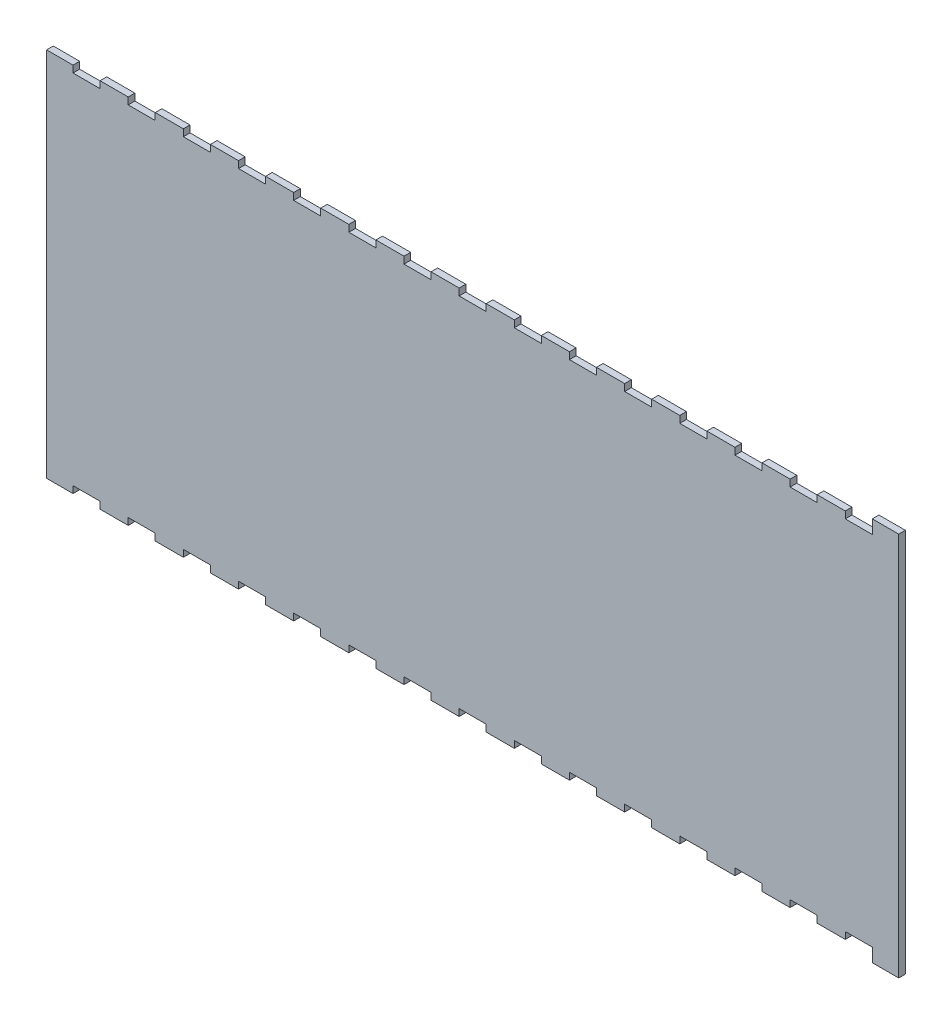
SolidWorks part; units mm, degrees
ref_plane "Front Plane" through (0, 0, 0) normal (0, 0, 1) x (1, 0, 0)
ref_plane "Top Plane" through (0, 0, 0) normal (0, 1, 0) x (1, 0, 0)
ref_plane "Right Plane" through (0, 0, 0) normal (1, 0, 0) x (0, 0, -1)
sketch "Sketch1" plane through (0, 0, 0) normal (0, 0, 1) x (1, 0, 0)
  line L248 (-12.6, 173.7122) -> (-25.5, 173.7122)
  line L249 (-25.5, 173.7122) -> (-25.5, 176.9872)
  line L250 (-25.5, 176.9872) -> (-38.9071, 176.9872)
  line L251 (-38.9071, 176.9872) -> (-38.9071, 173.7122)
  line L252 (-38.9071, 173.7122) -> (-51.8071, 173.7122)
  line L253 (-51.8071, 173.7122) -> (-51.8071, 176.9872)
  line L254 (-51.8071, 176.9872) -> (-65.2143, 176.9872)
  line L255 (-65.2143, 176.9872) -> (-65.2143, 173.7122)
  line L256 (-65.2143, 173.7122) -> (-78.1143, 173.7122)
  line L257 (-78.1143, 173.7122) -> (-78.1143, 176.9872)
  line L258 (-78.1143, 176.9872) -> (-91.5214, 176.9872)
  line L259 (-91.5214, 176.9872) -> (-91.5214, 173.7122)
  line L260 (-91.5214, 173.7122) -> (-104.4214, 173.7122)
  line L261 (-104.4214, 173.7122) -> (-104.4214, 176.9872)
  line L262 (-104.4214, 176.9872) -> (-117.8286, 176.9872)
  line L263 (-117.8286, 176.9872) -> (-117.8286, 173.7122)
  line L264 (-117.8286, 173.7122) -> (-130.7286, 173.7122)
  line L265 (-130.7286, 173.7122) -> (-130.7286, 176.9872)
  line L266 (-130.7286, 176.9872) -> (-144.1357, 176.9872)
  line L267 (-144.1357, 176.9872) -> (-144.1357, 173.7122)
  line L268 (-144.1357, 173.7122) -> (-157.0357, 173.7122)
  line L269 (-157.0357, 173.7122) -> (-157.0357, 176.9872)
  line L270 (-157.0357, 176.9872) -> (-170.4429, 176.9872)
  line L271 (-170.4429, 176.9872) -> (-170.4429, 173.7122)
  line L272 (-170.4429, 173.7122) -> (-183.3429, 173.7122)
  line L273 (-183.3429, 173.7122) -> (-183.3429, 176.9872)
  line L274 (-183.3429, 176.9872) -> (-196.75, 176.9872)
  line L275 (-196.75, 176.9872) -> (-196.75, 173.7122)
  line L276 (-196.75, 173.7122) -> (-209.65, 173.7122)
  line L277 (-209.65, 173.7122) -> (-209.65, 176.9872)
  line L278 (-209.65, 176.9872) -> (-223.0571, 176.9872)
  line L279 (-223.0571, 176.9872) -> (-223.0571, 173.7122)
  line L280 (-223.0571, 173.7122) -> (-235.9571, 173.7122)
  line L281 (-235.9571, 173.7122) -> (-235.9571, 176.9872)
  line L282 (-235.9571, 176.9872) -> (-249.3643, 176.9872)
  line L283 (-249.3643, 176.9872) -> (-249.3643, 173.7122)
  line L284 (-249.3643, 173.7122) -> (-262.2643, 173.7122)
  line L285 (-262.2643, 173.7122) -> (-262.2643, 176.9872)
  line L286 (-262.2643, 176.9872) -> (-275.6714, 176.9872)
  line L287 (-275.6714, 176.9872) -> (-275.6714, 173.7122)
  line L288 (-275.6714, 173.7122) -> (-288.5714, 173.7122)
  line L289 (-288.5714, 173.7122) -> (-288.5714, 176.9872)
  line L290 (-288.5714, 176.9872) -> (-301.9786, 176.9872)
  line L291 (-301.9786, 176.9872) -> (-301.9786, 173.7122)
  line L292 (-301.9786, 173.7122) -> (-314.8786, 173.7122)
  line L293 (-314.8786, 173.7122) -> (-314.8786, 176.9872)
  line L294 (-314.8786, 176.9872) -> (-328.2857, 176.9872)
  line L295 (-328.2857, 176.9872) -> (-328.2857, 173.7122)
  line L296 (-328.2857, 173.7122) -> (-341.1857, 173.7122)
  line L297 (-341.1857, 173.7122) -> (-341.1857, 176.9872)
  line L298 (-341.1857, 176.9872) -> (-354.5929, 176.9872)
  line L299 (-354.5929, 176.9872) -> (-354.5929, 173.7122)
  line L300 (-354.5929, 173.7122) -> (-367.4929, 173.7122)
  line L301 (-367.4929, 173.7122) -> (-367.4929, 176.9872)
  line L302 (-367.4929, 176.9872) -> (-380.9, 176.9872)
  line L303 (-380.9, 176.9872) -> (-380.9, 173.7122)
  line L304 (-380.9, 173.7122) -> (-393.8, 173.7122)
  line L305 (-393.8, 173.7122) -> (-393.8, 176.9872)
  line L306 (-393.8, 176.9872) -> (-406.4, 176.9872)
  line L307 (-406.4, 176.9872) -> (-406.4, 0)
  line L308 (-406.4, 0) -> (-393.8, 0)
  line L309 (-393.8, 0) -> (-393.8, 3.275)
  line L310 (-393.8, 3.275) -> (-380.9, 3.275)
  line L311 (-380.9, 3.275) -> (-380.9, 0)
  line L312 (-380.9, 0) -> (-367.4929, 0)
  line L313 (-367.4929, 0) -> (-367.4929, 3.275)
  line L314 (-367.4929, 3.275) -> (-354.5929, 3.275)
  line L315 (-354.5929, 3.275) -> (-354.5929, 0)
  line L316 (-354.5929, 0) -> (-341.1857, 0)
  line L317 (-341.1857, 0) -> (-341.1857, 3.275)
  line L318 (-341.1857, 3.275) -> (-328.2857, 3.275)
  line L319 (-328.2857, 3.275) -> (-328.2857, 0)
  line L320 (-328.2857, 0) -> (-314.8786, 0)
  line L321 (-314.8786, 0) -> (-314.8786, 3.275)
  line L322 (-314.8786, 3.275) -> (-301.9786, 3.275)
  line L323 (-301.9786, 3.275) -> (-301.9786, 0)
  line L324 (-301.9786, 0) -> (-288.5714, 0)
  line L325 (-288.5714, 0) -> (-288.5714, 3.275)
  line L326 (-288.5714, 3.275) -> (-275.6714, 3.275)
  line L327 (-275.6714, 3.275) -> (-275.6714, 0)
  line L328 (-275.6714, 0) -> (-262.2643, 0)
  line L329 (-262.2643, 0) -> (-262.2643, 3.275)
  line L330 (-262.2643, 3.275) -> (-249.3643, 3.275)
  line L331 (-249.3643, 3.275) -> (-249.3643, 0)
  line L332 (-249.3643, 0) -> (-235.9571, 0)
  line L333 (-235.9571, 0) -> (-235.9571, 3.275)
  line L334 (-235.9571, 3.275) -> (-223.0571, 3.275)
  line L335 (-223.0571, 3.275) -> (-223.0571, 0)
  line L336 (-223.0571, 0) -> (-209.65, 0)
  line L337 (-209.65, 0) -> (-209.65, 3.275)
  line L338 (-209.65, 3.275) -> (-196.75, 3.275)
  line L339 (-196.75, 3.275) -> (-196.75, 0)
  line L340 (-196.75, 0) -> (-183.3429, 0)
  line L341 (-183.3429, 0) -> (-183.3429, 3.275)
  line L342 (-183.3429, 3.275) -> (-170.4429, 3.275)
  line L343 (-170.4429, 3.275) -> (-170.4429, 0)
  line L344 (-170.4429, 0) -> (-157.0357, 0)
  line L345 (-157.0357, 0) -> (-157.0357, 3.275)
  line L346 (-157.0357, 3.275) -> (-144.1357, 3.275)
  line L347 (-144.1357, 3.275) -> (-144.1357, 0)
  line L348 (-144.1357, 0) -> (-130.7286, 0)
  line L349 (-130.7286, 0) -> (-130.7286, 3.275)
  line L350 (-130.7286, 3.275) -> (-117.8286, 3.275)
  line L351 (-117.8286, 3.275) -> (-117.8286, 0)
  line L352 (-117.8286, 0) -> (-104.4214, 0)
  line L353 (-104.4214, 0) -> (-104.4214, 3.275)
  line L354 (-104.4214, 3.275) -> (-91.5214, 3.275)
  line L355 (-91.5214, 3.275) -> (-91.5214, 0)
  line L356 (-91.5214, 0) -> (-78.1143, 0)
  line L357 (-78.1143, 0) -> (-78.1143, 3.275)
  line L358 (-78.1143, 3.275) -> (-65.2143, 3.275)
  line L359 (-65.2143, 3.275) -> (-65.2143, 0)
  line L360 (-65.2143, 0) -> (-51.8071, 0)
  line L361 (-51.8071, 0) -> (-51.8071, 3.275)
  line L362 (-51.8071, 3.275) -> (-38.9071, 3.275)
  line L363 (-38.9071, 3.275) -> (-38.9071, 0)
  line L364 (-38.9071, 0) -> (-25.5, 0)
  line L365 (-25.5, 0) -> (-25.5, 3.275)
  line L366 (-25.5, 3.275) -> (-12.6, 3.275)
  line L367 (-12.6, 3.275) -> (-12.6, -3.175)
  line L368 (-12.6, -3.175) -> (0, -3.175)
  line L369 (0, -3.175) -> (0, 180.1622)
  line L370 (0, 180.1622) -> (-12.6, 180.1622)
  line L371 (-12.6, 180.1622) -> (-12.6, 173.7122)
extrude "Boss-Extrude1" add sketch "Sketch1" along normal blind 3.175
